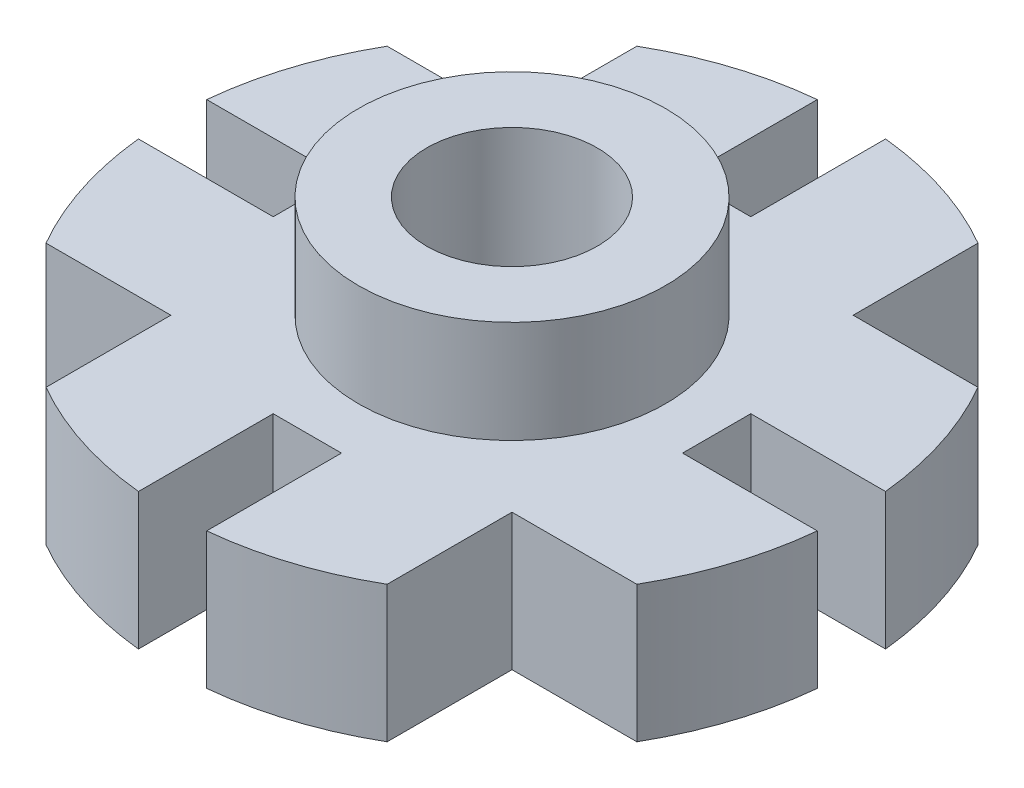
SolidWorks part; units mm, degrees
ref_plane "Front Plane" through (0, 0, 0) normal (0, 0, 1) x (1, 0, 0)
ref_plane "Top Plane" through (0, 0, 0) normal (0, 1, 0) x (1, 0, 0)
ref_plane "Right Plane" through (0, 0, 0) normal (1, 0, 0) x (0, 0, -1)
sketch "Sketch1" plane through (0, 0, 0) normal (0, 1, 0) x (1, 0, 0)
  circle A0 centre (0, 0) radius 63.5
  dimension "D1" = 127
extrude "Boss-Extrude1" add sketch "Sketch1" against normal blind 25.4
sketch "Sketch2" plane through (0, 0, 0) normal (0, 1, 0) x (1, 0, 0)
  circle A1 centre (0, 0) radius 28.575
  dimension "D1" = 57.15
extrude "Boss-Extrude2" add sketch "Sketch2" along normal blind 19.05
sketch "Sketch3" plane through (0, 0, 0) normal (0, 1, 0) x (1, 0, 0)
  line L0 (63.5, 6.35) -> (38.1, 6.35)
  line L1 (-6.35, 63.5) -> (6.35, 63.5)
  line L2 (-6.35, 63.5) -> (-6.35, 38.1)
  line L3 (-6.35, 38.1) -> (6.35, 38.1)
  line L4 (6.35, 63.5) -> (6.35, 38.1)
  line L5 (63.5, 6.35) -> (63.5, -6.35)
  line L6 (63.5, -6.35) -> (38.1, -6.35)
  line L7 (38.1, 6.35) -> (38.1, -6.35)
  line L8 (6.35, -63.5) -> (6.35, -38.1)
  line L9 (6.35, -63.5) -> (-6.35, -63.5)
  line L10 (-6.35, -63.5) -> (-6.35, -38.1)
  line L11 (6.35, -38.1) -> (-6.35, -38.1)
  line L12 (-63.5, -6.35) -> (-38.1, -6.35)
  line L13 (-63.5, -6.35) -> (-63.5, 6.35)
  line L14 (-63.5, 6.35) -> (-38.1, 6.35)
  line L15 (-38.1, -6.35) -> (-38.1, 6.35)
  point P4 (0, 63.5)
  point P5 (0, -63.5)
  point P6 (38.1, 0)
  point P19 (0, 0)
  point P24 (0, 38.1)
  dimension "D7" = 0
  dimension "D1" = 38.1
  dimension "D2" = 38.1
  dimension "D4" = 12.7
  dimension "D5" = 76.2
  dimension "D6" = 25.4
  dimension "D8" = 0
  dimension "D3" = 4
extrude "Cut-Extrude1" cut sketch "Sketch3" against normal through all
sketch "Sketch4" plane through (0, 0, 0) normal (0, 1, 0) x (1, 0, 0)
  line L0 (-6.35, 38.1) -> (6.35, 38.1) construction
  line L1 (-57.15, 57.15) -> (-31.75, 57.15)
  line L2 (-57.15, 57.15) -> (-57.15, 31.75)
  line L3 (-57.15, 31.75) -> (-31.75, 31.75)
  line L4 (-31.75, 57.15) -> (-31.75, 31.75)
  line L5 (-38.1, -6.35) -> (-38.1, 6.35) construction
  line L6 (57.15, 57.15) -> (31.75, 57.15)
  line L7 (57.15, 57.15) -> (57.15, 31.75)
  line L8 (57.15, 31.75) -> (31.75, 31.75)
  line L9 (31.75, 57.15) -> (31.75, 31.75)
  line L10 (57.15, -57.15) -> (57.15, -31.75)
  line L11 (57.15, -57.15) -> (31.75, -57.15)
  line L12 (31.75, -57.15) -> (31.75, -31.75)
  line L13 (57.15, -31.75) -> (31.75, -31.75)
  line L14 (-57.15, -57.15) -> (-31.75, -57.15)
  line L15 (-57.15, -57.15) -> (-57.15, -31.75)
  line L16 (-57.15, -31.75) -> (-31.75, -31.75)
  line L17 (-31.75, -57.15) -> (-31.75, -31.75)
  point P4 (-31.75, 44.45)
  point P7 (0, 38.1)
  point P10 (-38.1, 0)
  point P11 (0, 0)
  point P12 (0, 0)
  point P13 (0, 0)
  point P26 (0, 0)
  point P27 (0, 0)
  point P28 (57.15, 44.45)
  dimension "D1" = 25.4
  dimension "D2" = 25.4
  dimension "D3" = 31.75
  dimension "D4" = 31.75
  dimension "D6" = 44.45
  dimension "D7" = 44.9013
  dimension "D5" = 4
extrude "Cut-Extrude2" cut sketch "Sketch4" against normal through all
sketch "Sketch5" plane through (0, 19.05, 0) normal (0, 1, 0) x (1, 0, 0)
  circle A0 centre (0, 0) radius 15.875
  circle A2 centre (0, 0) radius 28.575 construction
  dimension "D1" = 12.7
extrude "Cut-Extrude3" cut sketch "Sketch5" against normal through all
equation "\"`\"=1.01468"
